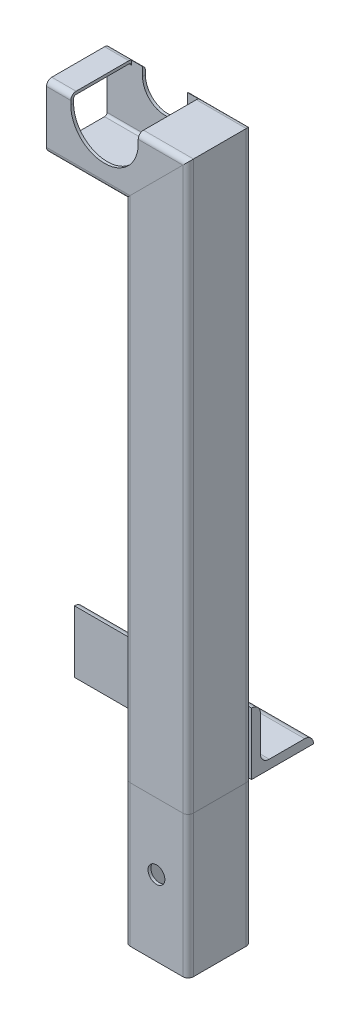
SolidWorks part; units mm, degrees
ref_plane "Front Plane" through (0, 0, 0) normal (0, 0, 1) x (1, 0, 0)
ref_plane "Top Plane" through (0, 0, 0) normal (0, 1, 0) x (1, 0, 0)
ref_plane "Right Plane" through (0, 0, 0) normal (1, 0, 0) x (0, 0, -1)
sketch "Sketch1" plane through (0, 0, 0) normal (0, 0, 1) x (1, 0, 0)
  line L0 (205.8375, 0) -> (205.8375, 302)
  line L1 (205.8375, 302) -> (143.7375, 302)
  line L2 (205.8375, 0) -> (205.8375, -80)
  line L3 (187.9375, 157.0549) -> (187.9375, -80) construction
  line L4 (192.7, 157.0549) -> (192.7, -80) construction
  line L5 (205.8375, 157.0549) -> (205.8375, -80) construction
  dimension "D1" = 302
  dimension "D2" = 80
  dimension "D3" = 62.1
  dimension "D4" = 4.7625
  dimension "D5" = 17.9
  dimension "D6" = 192.7
other "Structural MemberMain"
ref_plane "Plane1" through (205.8375, 0, 0) normal (0, 1, 0) x (-1, 0, 0)
sketch "Sketch11" plane through (205.8375, 0, 0) normal (0, 1, 0) x (-1, 0, 0)
  line L0 (-14.9, 16.3) -> (14.9, 16.3)
  line L1 (-14.9, 17.9) -> (14.9, 17.9)
  line L2 (-17.9, 14.9) -> (-17.9, -14.9)
  line L3 (-14.9, -17.9) -> (14.9, -17.9)
  line L4 (17.9, 14.9) -> (17.9, -14.9)
  line L5 (-17.9, 17.9) -> (17.9, -17.9) construction
  line L6 (-17.9, -17.9) -> (17.9, 17.9) construction
  line L7 (16.3, 14.9) -> (16.3, -14.9)
  line L8 (-14.9, -16.3) -> (14.9, -16.3)
  line L9 (-16.3, 14.9) -> (-16.3, -14.9)
  arc A0 (-17.9, -14.9) -> (-14.9, -17.9) centre (-14.9, -14.9) ccw
  arc A1 (14.9, -17.9) -> (17.9, -14.9) centre (14.9, -14.9) ccw
  arc A2 (17.9, 14.9) -> (14.9, 17.9) centre (14.9, 14.9) ccw
  arc A3 (-14.9, 17.9) -> (-17.9, 14.9) centre (-14.9, 14.9) ccw
  arc A4 (16.3, 14.9) -> (14.9, 16.3) centre (14.9, 14.9) ccw
  arc A5 (14.9, -16.3) -> (16.3, -14.9) centre (14.9, -14.9) ccw
  arc A6 (-16.3, -14.9) -> (-14.9, -16.3) centre (-14.9, -14.9) ccw
  arc A7 (-14.9, 16.3) -> (-16.3, 14.9) centre (-14.9, 14.9) ccw
  point P0 (0, 0)
  point P30 (0, 0)
  dimension "D3" = 3
  dimension "D1" = 35.8
  dimension "D2" = 35.8
  dimension "D4" = 1.6
sketch "Sketch12" plane through (0, 0, 0) normal (0, 0, 1) x (1, 0, 0)
  line L1 (176.5, 314.7) -> (176.5, 325.1) construction
  line L2 (163.8, 314.7) -> (163.8, 325.1)
  line L3 (189.2, 314.7) -> (189.2, 325.1)
  line L4 (205.8375, 302) -> (143.7375, 302) construction
  line L5 (143.7375, 319.9) -> (223.7375, 319.9) construction
  arc A0 (163.8, 314.7) -> (189.2, 314.7) centre (176.5, 314.7) ccw
  arc A1 (189.2, 325.1) -> (163.8, 325.1) centre (176.5, 325.1) ccw
  point P2 (176.5, 319.9)
  dimension "D1" = 25.4
  dimension "D2" = 176.5
extrude "Cut-ExtrudeTopRailGuide" cut sketch "Sketch12" against normal through all and the other way through all
sketch "Sketch13" plane through (0, 0, 0) normal (0, 1, 0) x (1, 0, 0)
  line L0 (123.7375, 17.9) -> (223.7375, 17.9)
  line L2 (189.2, 17.9) -> (220.7375, 17.9) construction
  line L3 (223.7375, 14.9) -> (223.7375, -14.9) construction
  point P4 (173.7375, 17.9)
  dimension "D1" = 100
other "Structural MemberAngle"
ref_plane "Plane2" through (123.7375, 0, -17.9) normal (1, 0, 0) x (0, 0, -1)
sketch "Sketch14" plane through (123.7375, 0, -17.9) normal (1, 0, 0) x (0, 0, -1)
  line L0 (0, 0) -> (0, 35)
  line L1 (0, 17.5) -> (5, 17.5) construction
  line L2 (5, 30) -> (5, 10)
  line L3 (10, 5) -> (30, 5)
  line L4 (17.5, 5) -> (17.5, 0) construction
  line L5 (35, 0) -> (0, 0)
  arc A0 (35, 0) -> (30, 5) centre (30, 0) ccw
  arc A1 (0, 35) -> (5, 30) centre (0, 30) cw
  arc A2 (10, 5) -> (5, 10) centre (10, 10) cw
  point P10 (17.5, 0)
  point P14 (0, 17.5)
  point P15 (5, 17.5)
  point P16 (17.5, 5)
  point P17 (5, 35)
  point P18 (35, 5)
  point P21 (0, 0)
  dimension "D2" = 5
  dimension "D3" = 35
  dimension "Radius_1" = 5
  dimension "D1" = 5
sketch "Sketch15" plane through (0, 0, 0) normal (0, 1, 0) x (1, 0, 0)
  line L2 (-65.8005, 37.9) -> (555.2755, 37.9) construction
  line L3 (123.7375, 17.9) -> (223.7375, 17.9) construction
  line L4 (0, 28.933) -> (0, -28.933) construction
  circle A0 centre (157.7, 37.9) radius 4.7625
  circle A1 centre (192.7, 37.9) radius 5.0441
  point P7 (244.7375, 37.9)
  point P16 (0, 0)
  dimension "D2" = 9.525
  dimension "D1" = 20
  dimension "D3" = 192.7
  dimension "D4" = 35
extrude "Cut-ExtrudeMountingHoles" cut sketch "Sketch15" along normal through all
sketch "Sketch16" plane through (0, 0, 0) normal (0, 0, 1) x (1, 0, 0)
  line L4 (195.55, 314.7) -> (195.55, 325.1)
  line L5 (157.45, 325.1) -> (157.45, 314.7)
  line L6 (195.55, 314.7) -> (195.55, 325.1)
  line L7 (157.45, 325.1) -> (157.45, 314.7)
  arc A4 (157.45, 314.7) -> (195.55, 314.7) centre (176.5, 314.7) ccw
  arc A5 (195.55, 325.1) -> (157.45, 325.1) centre (176.5, 325.1) ccw
  arc A6 (157.45, 314.7) -> (195.55, 314.7) centre (176.5, 314.7) ccw
  arc A7 (195.55, 325.1) -> (157.45, 325.1) centre (176.5, 325.1) ccw
  dimension "D1" = 6.35
extrude "Cut-ExtrudeEnlargeRailGuide" cut sketch "Sketch16" against normal up to surface and the other way through all
sketch "Sketch17" plane through (0, 0, 17.9) normal (0, 0, 1) x (1, 0, 0)
  line L0 (205.8375, -80) -> (205.8375, -37.5) construction
  line L1 (190.9375, -80) -> (220.7375, -80) construction
  line L2 (123.7375, 0) -> (223.7375, 0) construction
  line L3 (223.7375, 0) -> (223.7375, -80) construction
  circle A0 centre (205.8375, -37.5) radius 4.7625
  dimension "D1" = 9.525
  dimension "D2" = 37.5
  dimension "D3" = 17.9
extrude "Cut-Extrude1" cut sketch "Sketch17" against normal through all
